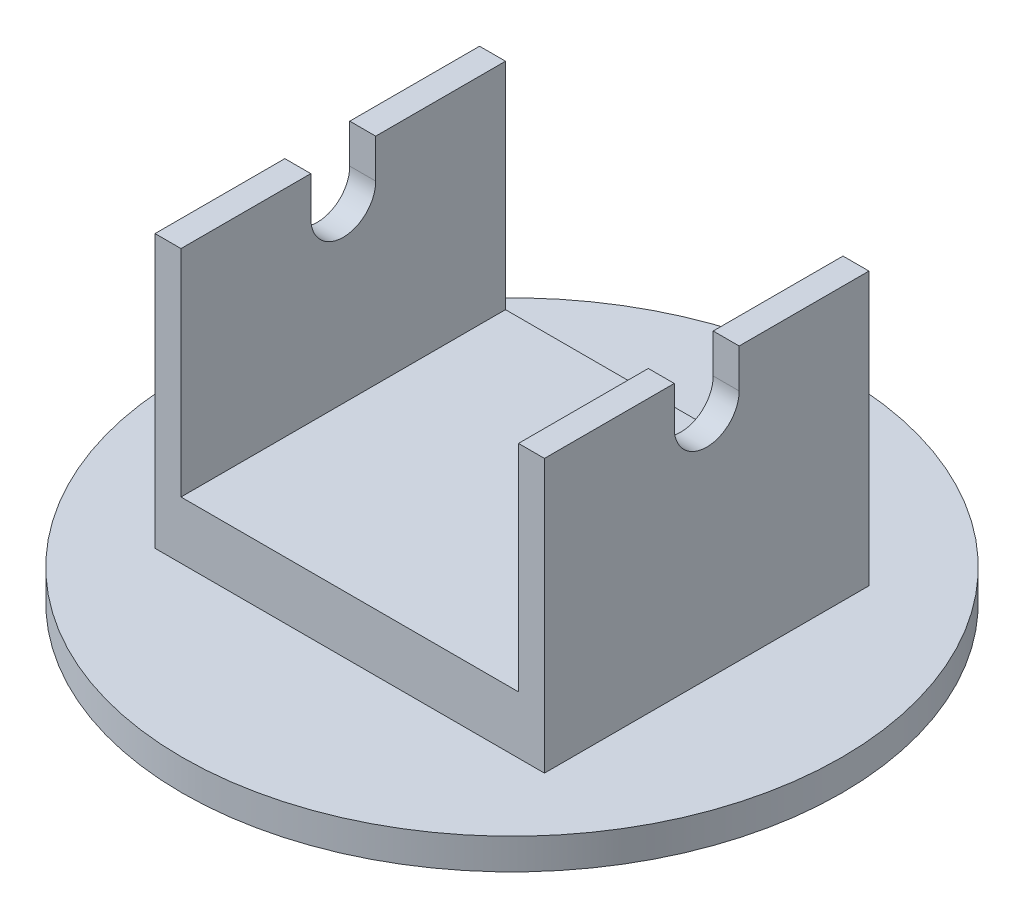
SolidWorks part; units mm, degrees
ref_plane "Front Plane" through (0, 0, 0) normal (0, 0, 1) x (1, 0, 0)
ref_plane "Top Plane" through (0, 0, 0) normal (0, 1, 0) x (1, 0, 0)
ref_plane "Right Plane" through (0, 0, 0) normal (1, 0, 0) x (0, 0, -1)
ref_plane "Plane1" through (0, 0, 0) normal (0, 1, 0) x (-1, 0, 0)
sketch "Sketch2" plane through (0, 0, 0) normal (0, 1, 0) x (-1, 0, 0)
  circle A0 centre (0, 0) radius 50.8
  dimension "D1" = 101.6
extrude "Boss-Extrude1" add sketch "Sketch2" along normal blind 4.7625
sketch "Sketch4" plane through (0, 0, 0) normal (1, 0, 0) x (0, 0, -1)
  line L0 (-25, 4.7625) -> (25, 4.7625)
  line L1 (50.8, 4.7625) -> (-50.8, 4.7625) construction
  line L2 (25, 4.7625) -> (16, 46.7625)
  line L3 (16, 46.7625) -> (-16, 46.7625)
  line L4 (-16, 46.7625) -> (-25, 4.7625)
  line L5 (0, 4.7625) -> (0, 0) construction
  line L6 (0, 4.7625) -> (0, 46.7625) construction
  dimension "D1" = 50
  dimension "D2" = 32
  dimension "D3" = 42
extrude "Boss-Extrude2" add sketch "Sketch4" along normal mid plane 60
sketch "Sketch7" plane through (0, 0, 0) normal (0, 1, 0) x (-1, 0, 0)
  line L1 (30, -25) -> (-30, -25)
  line L2 (30, -25) -> (30, 25)
  line L3 (30, 25) -> (-30, 25)
  line L4 (-30, -25) -> (-30, 25)
extrude "Boss-Extrude3" add sketch "Sketch7" along normal up to surface (46.7625 mm away) up to face at (0, 46.7625, 0)
sketch "Sketch6" plane through (30, 0, 0) normal (1, 0, 0) x (0, 0, -1)
  line L0 (5, 40.7625) -> (5, 46.7625)
  line L1 (25, 46.7625) -> (-25, 46.7625) construction
  line L2 (-5, 40.7625) -> (-5, 46.7625)
  line L3 (-25, 4.7625) -> (25, 4.7625) construction
  line L4 (-5, 46.7625) -> (5, 46.7625)
  arc A0 (-5, 40.7625) -> (5, 40.7625) centre (0, 40.7625) ccw
  dimension "D1" = 10
  dimension "D2" = 36
extrude "Cut-Extrude2" cut sketch "Sketch6" against normal through all
sketch "Sketch5" plane through (0, 0, 0) normal (0, 0, 1) x (1, 0, 0)
  line L1 (-26, 13.6088) -> (26, 13.6088)
  line L2 (-26, 13.6088) -> (-26, 46.7625)
  line L3 (-26, 46.7625) -> (26, 46.7625)
  line L4 (26, 13.6088) -> (26, 46.7625)
  line L5 (-26, 13.6088) -> (26, 46.7625) construction
  line L6 (-26, 46.7625) -> (26, 13.6088) construction
  line L12 (50.8, 4.7625) -> (-50.8, 4.7625) construction
  point P0 (0, 30.1856)
  dimension "D1" = 33.1537
  dimension "D2" = 52
  dimension "D3" = 8.8463
extrude "Cut-Extrude1" cut sketch "Sketch5" against normal through all and the other way through all
